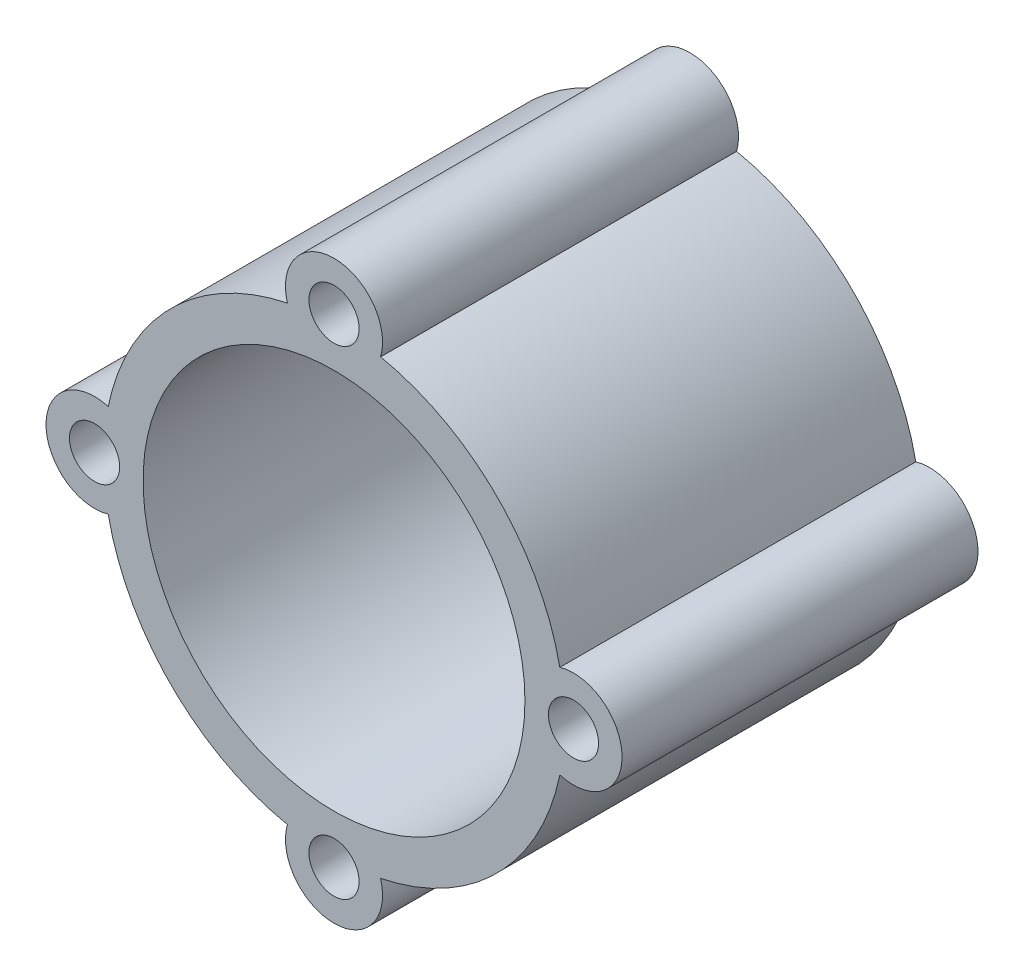
SolidWorks part; units mm, degrees
ref_plane "Front Plane" through (0, 0, 0) normal (0, 0, 1) x (1, 0, 0)
ref_plane "Top Plane" through (0, 0, 0) normal (0, 1, 0) x (1, 0, 0)
ref_plane "Right Plane" through (0, 0, 0) normal (1, 0, 0) x (0, 0, -1)
sketch "Sketch1" plane through (0, 0, 0) normal (0, 0, 1) x (1, 0, 0)
  circle A0 centre (0, 0) radius 28.5
  circle A1 centre (0, 0) radius 23.6
  dimension "D1" = 47.2
  dimension "D2" = 57
extrude "Boss-Extrude1" add sketch "Sketch1" along normal blind 44
sketch "Sketch2" plane through (0, 0, 0) normal (0, 0, -1) x (-1, 0, 0)
  line L0 (0, 29.6) -> (0, 0) construction
  circle A0 centre (0, 29.6) radius 6
  circle A1 centre (0, 0) radius 23.6 construction
  circle A2 centre (29.6, 0) radius 6
  circle A3 centre (0, -29.6) radius 6
  circle A4 centre (-29.6, 0) radius 6
  point P15 (0, 0)
  dimension "D1" = 12
  dimension "D2" = 4
extrude "Boss-Extrude2" add sketch "Sketch2" against normal up to surface (44 mm away) up to face at (28.5, 0, 44)
sketch "Sketch3" plane through (0, 0, 0) normal (0, 0, -1) x (-1, 0, 0)
  circle A0 centre (0, 29.6) radius 3.1
  circle A1 centre (29.6, 0) radius 3.1
  circle A2 centre (-29.6, 0) radius 3.1
  circle A3 centre (0, -29.6) radius 3.1
extrude "Cut-Extrude1" cut sketch "Sketch3" against normal through all
